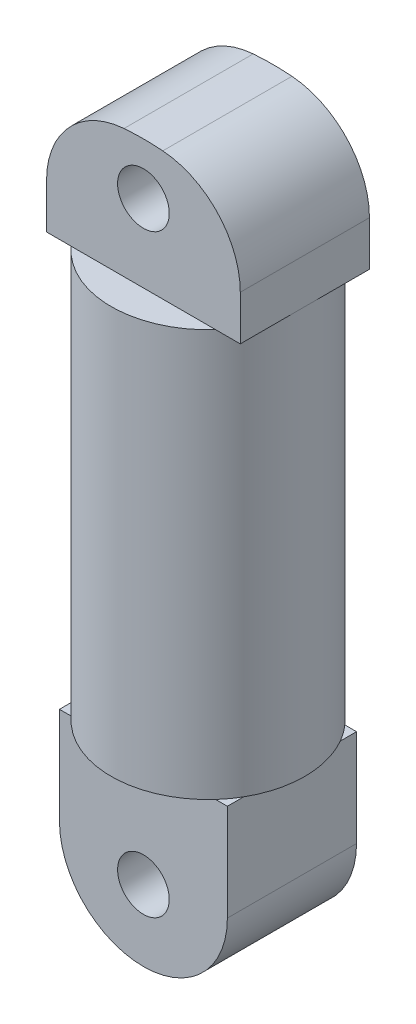
SolidWorks part; units mm, degrees
ref_plane "Front Plane" through (0, 0, 0) normal (0, 0, 1) x (1, 0, 0)
ref_plane "Top Plane" through (0, 0, 0) normal (0, 1, 0) x (1, 0, 0)
ref_plane "Right Plane" through (0, 0, 0) normal (1, 0, 0) x (0, 0, -1)
sketch "Sketch1" plane through (0, 0, 0) normal (0, 1, 0) x (1, 0, 0)
  circle A0 centre (0, 0) radius 15
  dimension "D1" = 30
extrude "Boss-Extrude1" add sketch "Sketch1" along normal blind 63
sketch "Sketch3" plane through (0, 0, 0) normal (0, 0, 1) x (1, 0, 0)
  line L0 (-13, 0) -> (-13, -15)
  line L1 (-15, 0) -> (15, 0) construction
  line L2 (13, 0) -> (13, -15)
  line L3 (0, 0) -> (0, -7.8405) construction
  line L4 (-13, 0) -> (13, 0)
  line L5 (15, 63) -> (-15, 63) construction
  line L7 (0, 60) -> (0, 67.8405) construction
  line L8 (-15, 63) -> (15, 63)
  line L9 (15, 63) -> (15, 69.923)
  line L10 (-15, 63) -> (-15, 69.923)
  line L11 (-15, 63) -> (-15, 0) construction
  line L12 (15, 0) -> (15, 63) construction
  arc A0 (-13, -15) -> (13, -15) centre (0, -15) ccw
  circle A1 centre (0, -17) radius 4
  circle A2 centre (0, 75) radius 4
  arc A3 (-3, 82.8844) -> (3, 82.8844) centre (0, 44) cw
  arc A4 (-3, 82.8844) -> (-15, 69.923) centre (-2, 69.923) ccw
  arc A5 (3, 82.8844) -> (15, 69.923) centre (2, 69.923) cw
  point P13 (0, 83)
  point P31 (-15, 80)
  point P34 (15, 80)
  dimension "D1" = 13
  dimension "D3" = 8
  dimension "D7" = 8
  dimension "D9" = 13
  dimension "D2" = 15
  dimension "D4" = 17
  dimension "D5" = 20
  dimension "D6" = 17
  dimension "D8" = 12
extrude "Boss-Extrude2" add sketch "Sketch3" along normal mid plane 20
